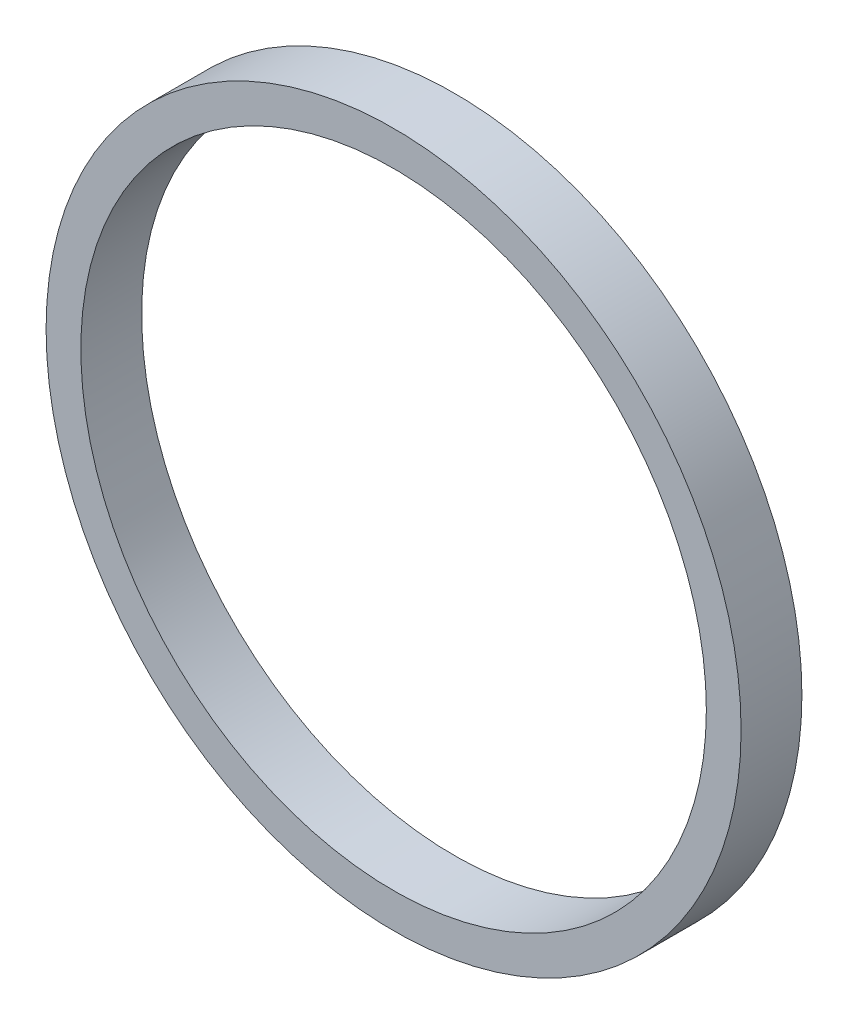
SolidWorks part; units mm, degrees
material "6061-T6 (SS)"
ref_plane "Ebene vorne" through (0, 0, 0) normal (0, 0, 1) x (1, 0, 0)
ref_plane "Ebene oben" through (0, 0, 0) normal (0, 1, 0) x (1, 0, 0)
ref_plane "Ebene rechts" through (0, 0, 0) normal (1, 0, 0) x (0, 0, -1)
sketch "Sketch1" plane through (0, 0, 0) normal (0, 0, 1) x (1, 0, 0)
  circle A0 centre (0, 0) radius 36
  circle A1 centre (0, 0) radius 40
  dimension "D1" = 4
  dimension "D2" = 72
extrude "Boss-Extrude1" add sketch "Sketch1" along normal blind 7
